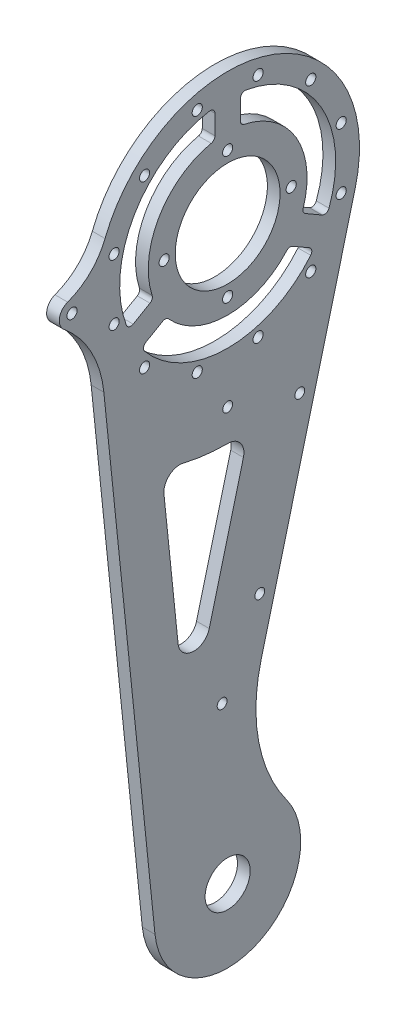
SolidWorks part; units mm, degrees
material "Thornel Mat VMA"
ref_plane "前视基准面" through (0, 0, 0) normal (0, 0, 1) x (1, 0, 0)
ref_plane "上视基准面" through (0, 0, 0) normal (0, 1, 0) x (1, 0, 0)
ref_plane "右视基准面" through (0, 0, 0) normal (1, 0, 0) x (0, 0, -1)
sketch "草图1" plane through (0, 0, 0) normal (1, 0, 0) x (0, 0, -1)
  line L0 (40.1598, -10.4615) -> (1.9651, -157.0841)
  line L1 (-41.2802, -4.2653) -> (-22.8782, -182.3639)
  circle A0 centre (0, 0) radius 41.5
  circle A1 centre (0, -180) radius 23
  dimension "D1" = 83
  dimension "D2" = 46
  dimension "D3" = 180
  dimension "D4" = 20.5
extrude "凸台-拉伸1" add sketch "草图1" along normal blind 4 contours A0 | A1 L0 A0 L1 | A1
sketch "草图3" plane through (0, 0, 0) normal (-1, 0, 0) x (0, 0, 1)
  circle A0 centre (0, 0) radius 34
  circle A1 centre (0, -180) radius 7.1
  arc A2 (-1.9651, -157.0841) -> (22.8782, -182.3639) centre (0, -180) ccw construction
  dimension "D1" = 68
  dimension "D2" = 14.2
extrude "切除-拉伸2" cut sketch "草图3" against normal blind 4
sketch "草图2" plane through (0, 0, 0) normal (-1, 0, 0) x (0, 0, 1)
  line L0 (-9.5763, 35.7393) -> (0, 0) construction
  line L1 (0, 0) -> (34, 0) construction
  circle A0 centre (0, 0) radius 37
  circle A1 centre (-9.5763, 35.7393) radius 1.6
  circle A2 centre (0, 0) radius 34 construction
  point P10 (0, 37)
  dimension "D1" = 74
  dimension "D2" = 3.2
  dimension "D3" = 105
extrude "切除-拉伸1" cut sketch "草图2" against normal blind 4 contours A0 A1 | A0 A1
pattern_circular "阵列(圆周)1" count 12 over 360 about axis through (0, 0, 0) along (1, 0, 0) of "切除-拉伸1"
fillet "圆角1" radius 50 1 edges at (2, -157.0841, -1.9651)
sketch "草图4" plane through (4, 0, 0) normal (1, 0, 0) x (0, 0, -1)
  line L0 (-37, 0) -> (-49, 0) construction
  line L1 (-37, -4) -> (-49, -4)
  line L2 (-37, 4) -> (-49, 4)
  arc A0 (-37, -4) -> (-37, 4) centre (-37, 0) ccw
  arc A1 (-49, 4) -> (-49, -4) centre (-49, 0) ccw
  circle A2 centre (0, 0) radius 34 construction
  circle A3 centre (-49, 0) radius 1.6
  point P2 (-43, 0)
  dimension "D1" = 4
  dimension "D2" = 37
  dimension "D3" = 3.2
  dimension "D4" = 12
extrude "凸台-拉伸2" add sketch "草图4" against normal up to surface (4 mm away)
fillet "圆角2" radius 20 1 edges at (2, 4, 41.3068)
sketch "草图5" plane through (4, 0, 0) normal (1, 0, 0) x (0, 0, -1)
  line L1 (22.7171, -57.5863) -> (10.1129, -105.9716) construction
  line L2 (24.217, -57.9771) -> (22.7171, -57.5863) construction
  line L4 (40.1598, -10.4615) -> (10.5134, -124.2687) construction
  circle A1 centre (22.7171, -57.5863) radius 1.55
  circle A3 centre (10.1129, -105.9716) radius 1.55
  circle A6 centre (0, 0) radius 34 construction
  point P10 (25.3366, -67.3651)
  dimension "D1" = 3.1
  dimension "D2" = 50
  dimension "D4" = 3.1
  dimension "D5" = 5
  dimension "D8" = 50
extrude "切除-拉伸3" cut sketch "草图5" against normal blind 44
sketch "草图6" plane through (4, 0, 0) normal (1, 0, 0) x (0, 0, -1)
  line L0 (0, -50) -> (0, 0) construction
  circle A2 centre (0, -50) radius 1.55
  circle A3 centre (0, 0) radius 34 construction
  dimension "D3" = 50
  dimension "D4" = 3.1
extrude "切除-拉伸4" cut sketch "草图6" against normal up to vertex (4 mm away) up to point (0, 0, 0)
sketch "草图7" plane through (0, 0, 0) normal (-1, 0, 0) x (0, 0, 1)
  line L0 (-4, 33.7639) -> (-4, 24.6779)
  line L1 (4, 33.7639) -> (4, 24.6779)
  line L2 (0, 0) -> (0, 34) construction
  line L3 (0, 0) -> (29.4449, -17) construction
  line L4 (0, 0) -> (-29.4449, -17) construction
  line L5 (23.3717, -8.8749) -> (31.2404, -13.4178)
  line L6 (19.3717, -15.8031) -> (27.2404, -20.346)
  line L7 (-23.3717, -8.8749) -> (-31.2404, -13.4178)
  line L8 (-19.3717, -15.8031) -> (-27.2404, -20.346)
  arc A0 (27.2404, -20.346) -> (31.2404, -13.4178) centre (0, 0) ccw
  circle A1 centre (0, 0) radius 34 construction
  circle A2 centre (0, 0) radius 25
  arc A3 (27.2404, -20.346) -> (31.2404, -13.4178) centre (0, 0) ccw
  arc A4 (-31.2404, -13.4178) -> (-27.2404, -20.346) centre (0, 0) ccw
  arc A5 (-31.2404, -13.4178) -> (-27.2404, -20.346) centre (0, 0) ccw
  arc A6 (4, 33.7639) -> (-4, 33.7639) centre (0, 0) ccw
  arc A7 (4, 33.7639) -> (-4, 33.7639) centre (0, 0) ccw
  circle A8 centre (0, 0) radius 16.5
  circle M28 centre (0, 0) radius 34
  dimension "D3" = 50
  dimension "D8" = 33
  dimension "D1" = 8
  dimension "D2" = 4
  dimension "D4" = 120
  dimension "D5" = 120
  dimension "D6" = 8
  dimension "D7" = 8
extrude "凸台-拉伸3" add sketch "草图7" against normal blind 4 contours A2 L1 L0 M28 | A2 | A2 L7 L8 M28 | A2 L6 L5 M28
sketch "草图8" plane through (4, 0, 0) normal (1, 0, 0) x (0, 0, -1)
  circle A0 centre (0, 0) radius 20
  arc A1 (23.3717, -8.8749) -> (4, 24.6779) centre (0, 0) ccw construction
  circle A2 centre (0, 20) radius 1.6
  dimension "D1" = 40
  dimension "D2" = 3.2
extrude "切除-拉伸5" cut sketch "草图8" against normal blind 5 contours A0 A2 | A0 A2
pattern_circular "阵列(圆周)3" count 4 over 360 about axis through (0, 0, 0) along (1, 0, 0) of "切除-拉伸5"
fillet "圆角3" radius 1.5 12 edges at (2, 24.6779, 4) (2, 33.7639, 4) (2, -8.8749, 23.3717) (2, -13.4178, 31.2404) (2, -20.346, 27.2404) (2, -15.8031, 19.3717) (2, -15.8031, -19.3717) (2, -20.346, -27.2404) (2, -8.8749, -23.3717) (2, -13.4178, -31.2404) (2, 24.6779, -4) (2, 33.7639, -4)
sketch "草图9" plane through (4, 0, 0) normal (1, 0, 0) x (0, 0, -1)
  line L0 (0, -180) -> (-1.746, -130) construction
  line L1 (0, -180) -> (0, 0) construction
  circle A0 centre (-1.746, -130) radius 1.55
  circle A1 centre (0, -180) radius 7.1 construction
  dimension "D3" = 3.1
  dimension "D2" = 50
  dimension "D1" = 2
extrude "切除-拉伸6" cut sketch "草图9" against normal blind 10
fillet "圆角4" radius 35 1 edges at (2, -4, 41.3068)
sketch "草图10" plane through (4, 0, 0) normal (1, 0, 0) x (0, 0, -1)
  line L0 (-20.8271, -56.2693) -> (-12.7653, -134.2928)
  line L1 (-12.7653, -134.2928) -> (6.685, -59.6264)
  line L3 (-38.9824, -26.5044) -> (-22.8782, -182.3639) construction
  line L4 (40.1598, -10.4615) -> (10.5134, -124.2687) construction
  arc A0 (-20.8271, -56.2693) -> (6.685, -59.6264) centre (0, 0) ccw
  arc A1 (-26.1432, -21.7378) -> (26.1432, -21.7378) centre (0, 0) ccw construction
  dimension "D1" = 60
  dimension "D2" = 20
  dimension "D3" = 15
extrude "切除-拉伸7" cut sketch "草图10" against normal blind 10
fillet "圆角5" radius 5 3 edges at (2, -56.2693, 20.8271) (2, -59.6264, -6.685) (2, -134.2928, 12.7653)
